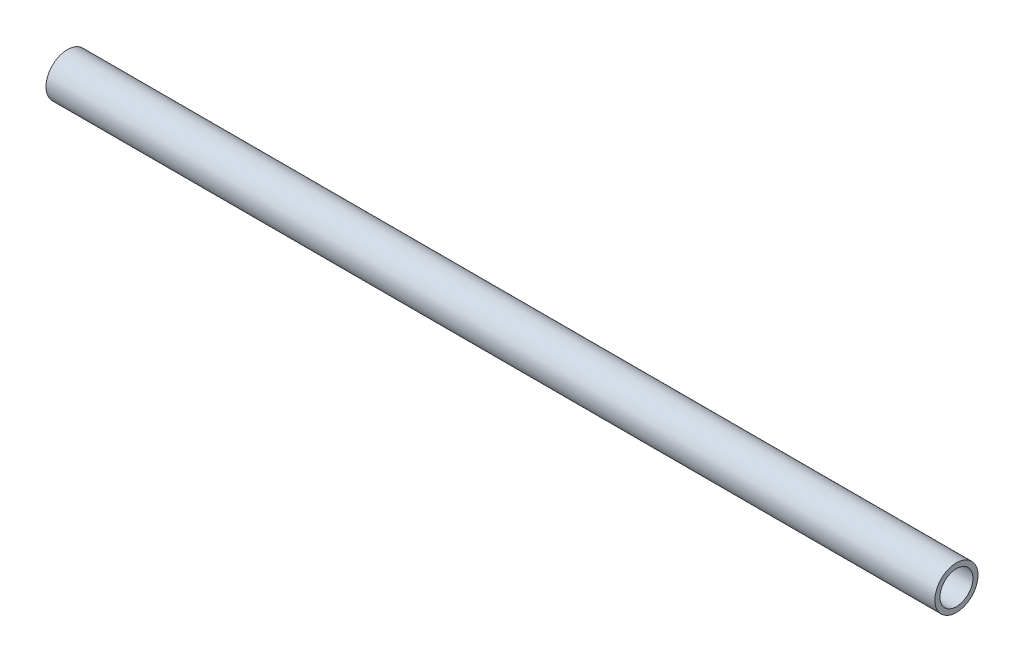
SolidWorks part; units mm, degrees
ref_plane "Front Plane" through (0, 0, 0) normal (0, 0, 1) x (1, 0, 0)
ref_plane "Top Plane" through (0, 0, 0) normal (0, 1, 0) x (1, 0, 0)
ref_plane "Right Plane" through (0, 0, 0) normal (1, 0, 0) x (0, 0, -1)
sketch "Sketch1" plane through (0, 0, 0) normal (1, 0, 0) x (0, 0, -1)
  circle A0 centre (0, 0) radius 8
  circle A1 centre (0, 0) radius 6.1148
  dimension "D1" = 16
extrude "Boss-Extrude1" add sketch "Sketch1" along normal blind 330
